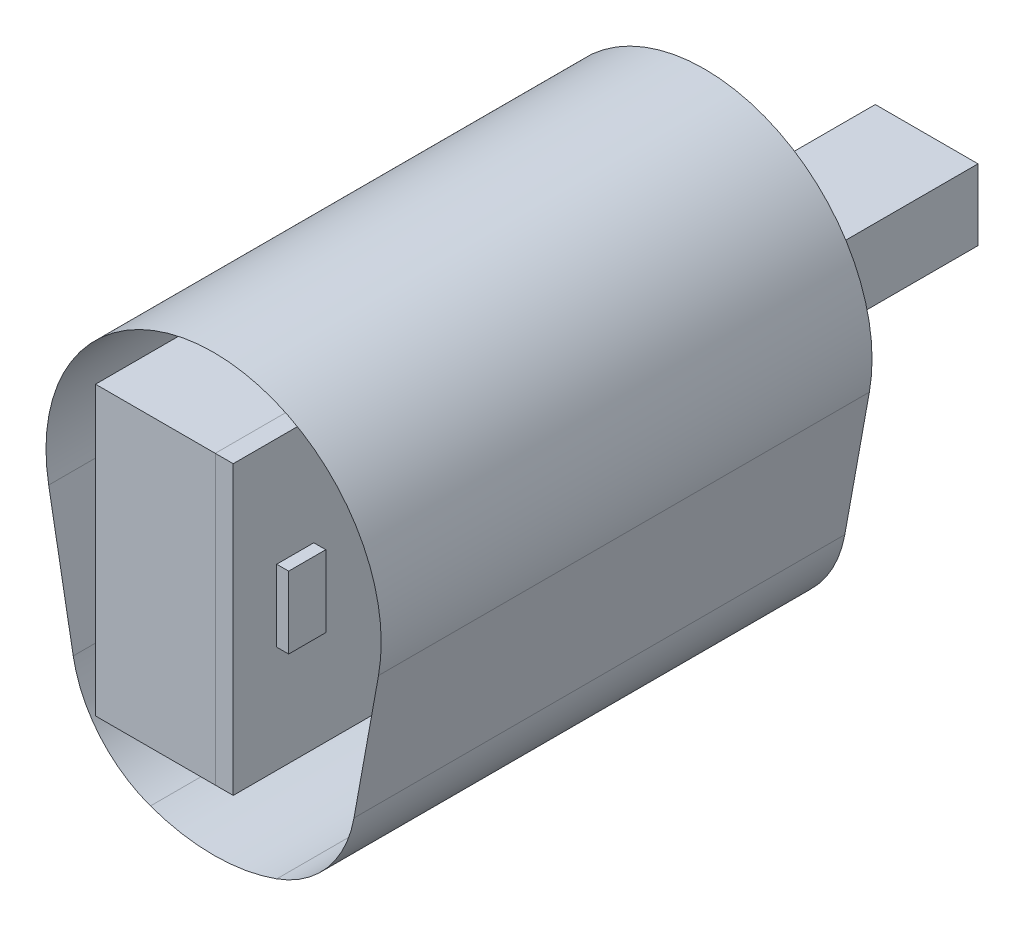
SolidWorks part; units mm, degrees
ref_plane "Front Plane" through (0, 0, 0) normal (0, 0, 1) x (1, 0, 0)
ref_plane "Top Plane" through (0, 0, 0) normal (0, 1, 0) x (1, 0, 0)
ref_plane "Right Plane" through (0, 0, 0) normal (1, 0, 0) x (0, 0, -1)
sketch "Sketch1" plane through (0, 0, 0) normal (1, 0, 0) x (0, 0, -1)
  line L1 (10.0873, 15.1707) -> (31.0873, 15.1707)
  line L2 (10.0873, 15.1707) -> (10.0873, 27.1707)
  line L3 (10.0873, 27.1707) -> (31.0873, 27.1707)
  line L4 (31.0873, 15.1707) -> (31.0873, 27.1707)
  dimension "D1" = 21
  dimension "D2" = 12
extrude "battery" add sketch "Sketch1" along normal blind 5
ref_plane "Plane1" through (0, 0, -33.0073) normal (0, 0, -1) x (-1, 0, 0)
sketch "Sketch2" plane through (0, 0, -33.0073) normal (0, 0, -1) x (-1, 0, 0)
  line L1 (-2.7858, 20.8301) -> (-7.0758, 20.8301)
  line L2 (-2.7858, 20.8301) -> (-2.7858, 23.7901)
  line L3 (-2.7858, 23.7901) -> (-7.0758, 23.7901)
  line L4 (-7.0758, 20.8301) -> (-7.0758, 23.7901)
  dimension "D1" = 4.29
  dimension "D2" = 2.96
extrude "driver" add sketch "Sketch2" along normal blind 6.86 separate body
sketch "Sketch3" plane through (0, 0, -10.0873) normal (0, 0, 1) x (1, 0, 0)
  line L0 (-1.2361, 23.3253) -> (0.7568, 12.553)
  line L1 (3.6781, 24.2344) -> (3.6781, 8.5861) construction
  line L2 (8.5924, 23.3253) -> (6.5995, 12.553)
  arc A0 (8.5924, 23.3253) -> (-1.2361, 23.3253) centre (3.6781, 24.2344) ccw
  arc A1 (0.7568, 12.553) -> (6.5995, 12.553) centre (3.6781, 13.0935) ccw
sketch "Sketch6" plane through (5, 0, 0) normal (1, 0, 0) x (0, 0, -1)
  line L1 (31.0873, 27.1707) -> (10.0873, 27.1707)
  line L2 (31.0873, 27.1707) -> (31.0873, 15.1707)
  line L3 (31.0873, 15.1707) -> (10.0873, 15.1707)
  line L4 (10.0873, 27.1707) -> (10.0873, 15.1707)
extrude "pcb board" add sketch "Sketch6" along normal blind 0.75 separate body
sketch "Sketch7" plane through (5.75, 0, 0) normal (1, 0, 0) x (0, 0, -1)
  line L1 (31.0873, 27.1707) -> (18.3873, 27.1707)
  line L2 (31.0873, 27.1707) -> (31.0873, 18.2707)
  line L3 (31.0873, 18.2707) -> (18.3873, 18.2707)
  line L4 (18.3873, 27.1707) -> (18.3873, 18.2707)
  dimension "D1" = 12.7
  dimension "D2" = 8.9
extrude "KLR device" add sketch "Sketch7" along normal blind 2 separate body
sketch "Sketch8" plane through (5.75, 0, 0) normal (1, 0, 0) x (0, 0, -1)
  line L1 (11.9029, 22.6273) -> (13.4529, 22.6273)
  line L2 (11.9029, 22.6273) -> (11.9029, 19.6273)
  line L3 (11.9029, 19.6273) -> (13.4529, 19.6273)
  line L4 (13.4529, 22.6273) -> (13.4529, 19.6273)
  dimension "D1" = 3
  dimension "D2" = 1.55
extrude "antenna" add sketch "Sketch8" along normal blind 0.5 separate body
sketch "Sketch9" plane through (0, 0, -10.0873) normal (0, 0, 1) x (1, 0, 0)
  line L0 (4.9308, 23.7901) -> (4.9308, 28.9916) construction
  line L1 (2.7858, 23.7901) -> (7.0758, 23.7901) construction
  line L2 (4.9308, 23.7901) -> (4.9308, 13.9391) construction
  line L4 (-0.932, 16.8763) -> (-1.9574, 22.5438)
  line L5 (10.7935, 16.8763) -> (11.8189, 22.5438)
  arc A0 (11.8189, 22.5438) -> (-1.9574, 22.5438) centre (4.9308, 23.7901) ccw
  arc A1 (10.7935, 16.8763) -> (7.5684, 13.0626) centre (5.8734, 17.7665) cw
  arc A2 (2.2931, 13.0626) -> (7.5684, 13.0626) centre (4.9308, 20.3823) ccw
  arc A3 (-0.932, 16.8763) -> (2.2931, 13.0626) centre (3.9882, 17.7665) ccw
  point P7 (10.4324, 14.8807)
  point P15 (-0.5709, 14.8807)
  dimension "D1" = 14
  dimension "D2" = 5
surface "Surface-Extrude1" sketch "Sketch9" parameters "D1"=20.5
